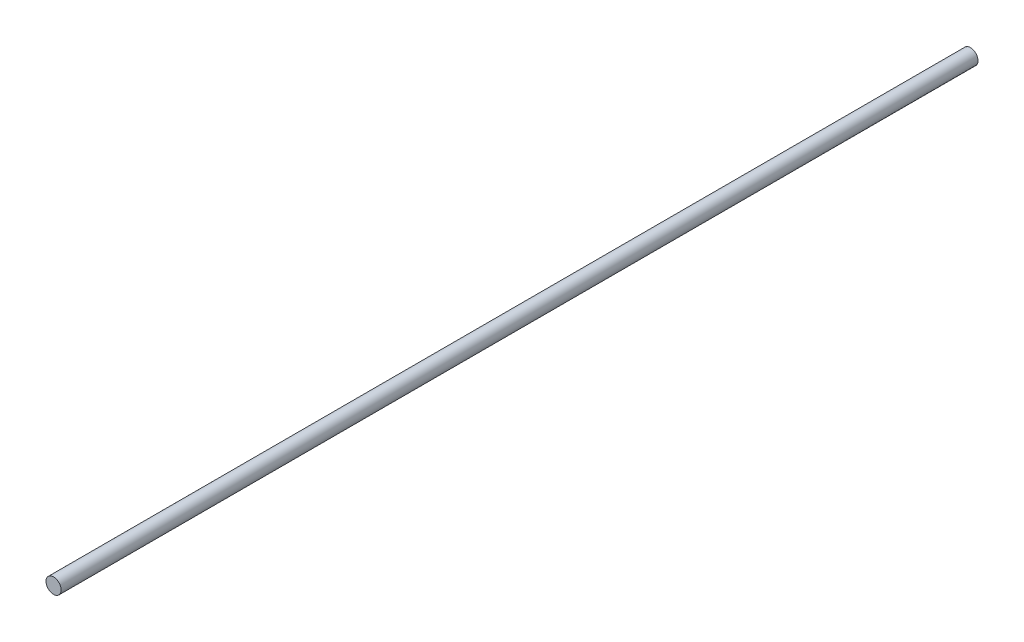
SolidWorks part; units mm, degrees
material "Liga 1060"
ref_plane "Plano frontal" through (0, 0, 0) normal (0, 0, 1) x (1, 0, 0)
ref_plane "Plano superior" through (0, 0, 0) normal (0, 1, 0) x (1, 0, 0)
ref_plane "Plano direito" through (0, 0, 0) normal (1, 0, 0) x (0, 0, -1)
sketch "Esboço1" plane through (0, 0, 0) normal (0, 0, 1) x (1, 0, 0)
  circle A0 centre (0, 0) radius 3.97
  dimension "D1" = 7.94
extrude "Ressalto-extrusão1" add sketch "Esboço1" along normal mid plane 480
